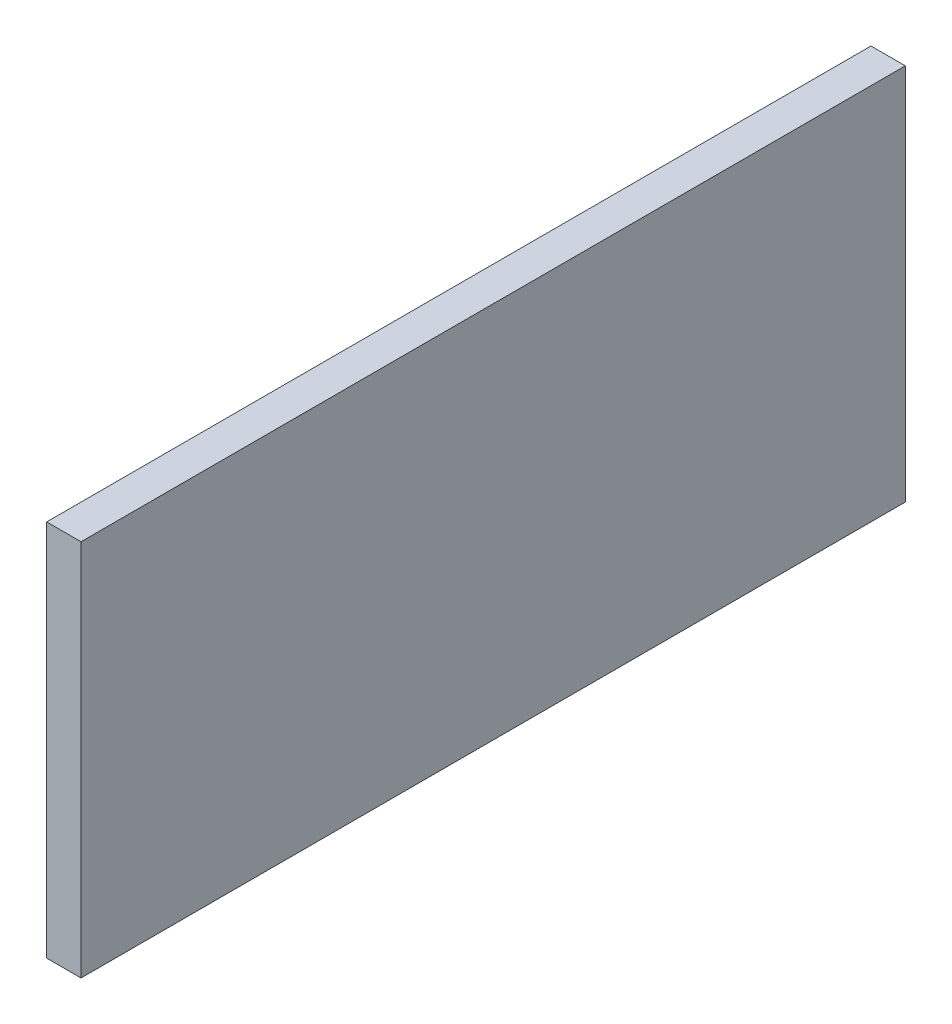
SolidWorks part; units mm, degrees
ref_plane "Front Plane" through (0, 0, 0) normal (0, 0, 1) x (1, 0, 0)
ref_plane "Top Plane" through (0, 0, 0) normal (0, 1, 0) x (1, 0, 0)
ref_plane "Right Plane" through (0, 0, 0) normal (1, 0, 0) x (0, 0, -1)
sketch "Sketch1" plane through (0, 0, 0) normal (1, 0, 0) x (0, 0, -1)
  line L1 (-152.4, 69.85) -> (152.4, 69.85)
  line L2 (-152.4, 69.85) -> (-152.4, -69.85)
  line L3 (-152.4, -69.85) -> (152.4, -69.85)
  line L4 (152.4, 69.85) -> (152.4, -69.85)
  line L5 (-152.4, 69.85) -> (152.4, -69.85) construction
  line L6 (-152.4, -69.85) -> (152.4, 69.85) construction
  point P0 (0, 0)
  dimension "D1" = 304.8
  dimension "D2" = 139.7
extrude "Boss-Extrude1" add sketch "Sketch1" along normal blind 12.7
